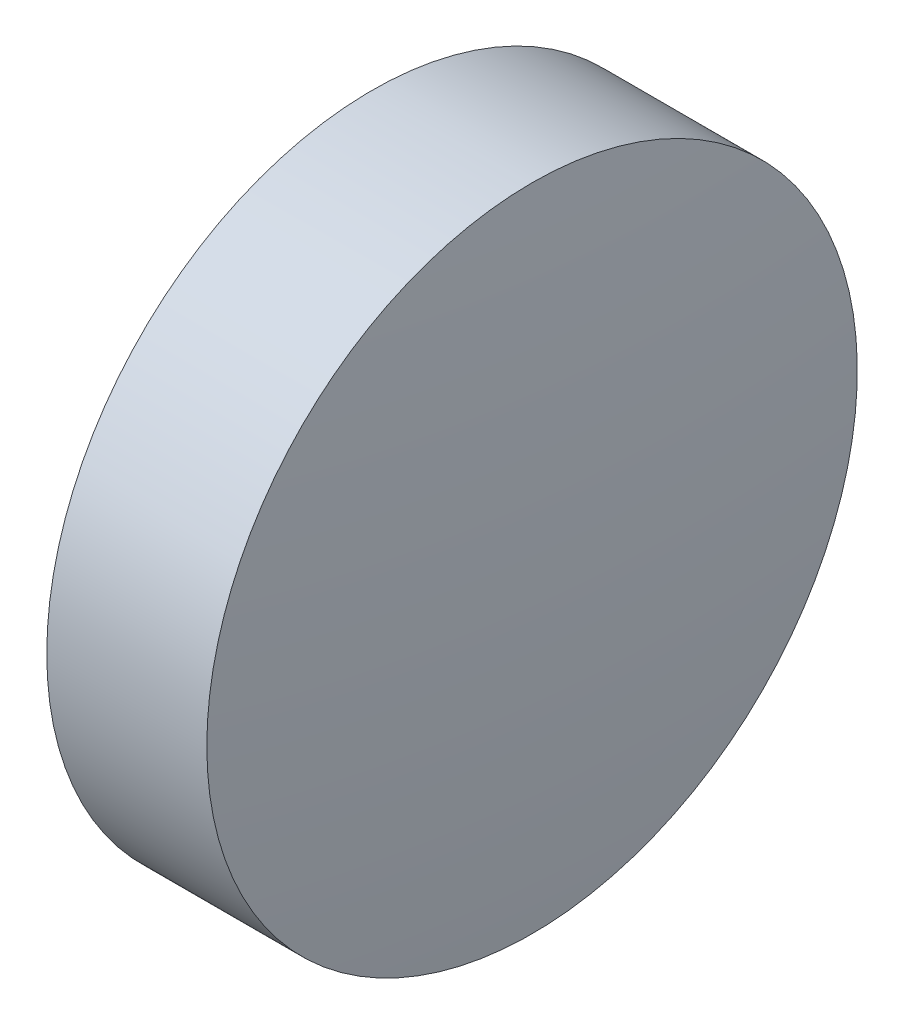
SolidWorks part; units mm, degrees
ref_plane "前视基准面" through (0, 0, 0) normal (0, 0, 1) x (1, 0, 0)
ref_plane "上视基准面" through (0, 0, 0) normal (0, 1, 0) x (1, 0, 0)
ref_plane "右视基准面" through (0, 0, 0) normal (1, 0, 0) x (0, 0, -1)
sketch "草图2" plane through (0, 0, 0) normal (0, 0, 1) x (1, 0, 0)
  line L0 (1116.2719, 408.8643) -> (1121.6502, 408.8643) construction
  line L1 (1116.7615, 408.8643) -> (1116.7615, 412.0143)
  line L2 (1116.7615, 412.0143) -> (1118.3115, 412.0143)
  line L3 (1116.7615, 408.8643) -> (1118.4615, 408.8643)
  arc A0 (1118.4615, 408.8643) -> (1118.3115, 412.0143) centre (1085.3115, 408.8643) ccw
revolve "旋转1" add sketch "草图2" angle 360 about L0
